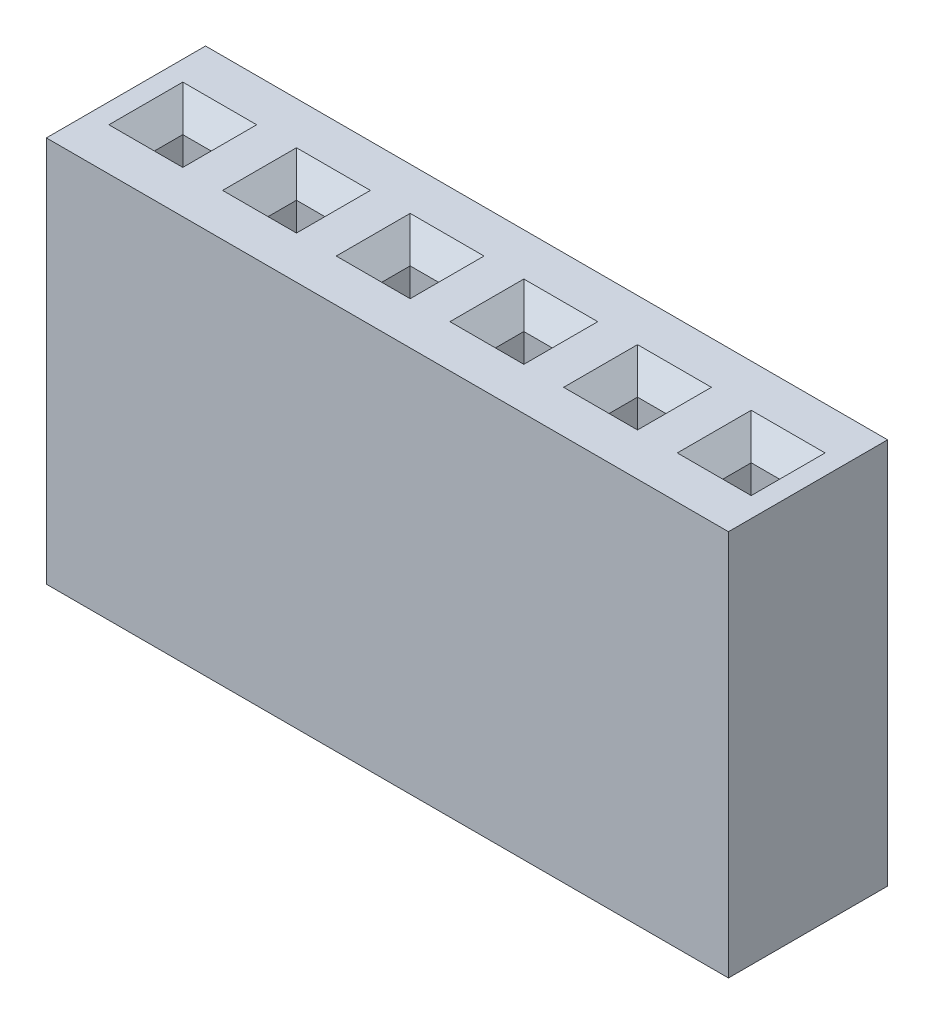
SolidWorks part; units mm, degrees
material "ABS PC"
ref_plane "Front Plane" through (0, 0, 0) normal (0, 0, 1) x (1, 0, 0)
ref_plane "Top Plane" through (0, 0, 0) normal (0, 1, 0) x (1, 0, 0)
ref_plane "Right Plane" through (0, 0, 0) normal (1, 0, 0) x (0, 0, -1)
sketch "Sketch1" plane through (0, 0, 0) normal (0, 1, 0) x (1, 0, 0)
  line L1 (0, 0) -> (15.24, 0)
  line L2 (0, 0) -> (0, 3.556)
  line L3 (0, 3.556) -> (15.24, 3.556)
  line L4 (15.24, 0) -> (15.24, 3.556)
  dimension "D1" = 3.556
  dimension "D2" = 15.24
extrude "Boss-Extrude1" add sketch "Sketch1" along normal blind 8.636
sketch "Sketch2" plane through (0, 8.636, 0) normal (0, 1, 0) x (1, 0, 0)
  line L0 (0, 0) -> (15.24, 0) construction
  line L1 (0.9525, 2.0955) -> (1.5875, 2.0955)
  line L2 (0.9525, 2.0955) -> (0.9525, 1.4605)
  line L3 (0.9525, 1.4605) -> (1.5875, 1.4605)
  line L4 (1.5875, 2.0955) -> (1.5875, 1.4605)
  line L5 (0.9525, 2.0955) -> (1.5875, 1.4605) construction
  line L6 (0.9525, 1.4605) -> (1.5875, 2.0955) construction
  line L7 (0, 3.556) -> (0, 0) construction
  point P0 (1.27, 1.778)
  dimension "D1" = 0.635
  dimension "D2" = 0.635
  dimension "D3" = 1.778
  dimension "D4" = 1.27
extrude "Cut-Extrude1" cut sketch "Sketch2" against normal blind 6.35
chamfer "Chamfer1" distance 0.508 angle 45 4 edges at (0.9525, 8.636, -1.778) (1.27, 8.636, -1.4605) (1.5875, 8.636, -1.778) (1.27, 8.636, -2.0955)
pattern_linear "LPattern1" count 6 spacing 2.54 along (1, 0, 0) of "Cut-Extrude1", "Chamfer1"
